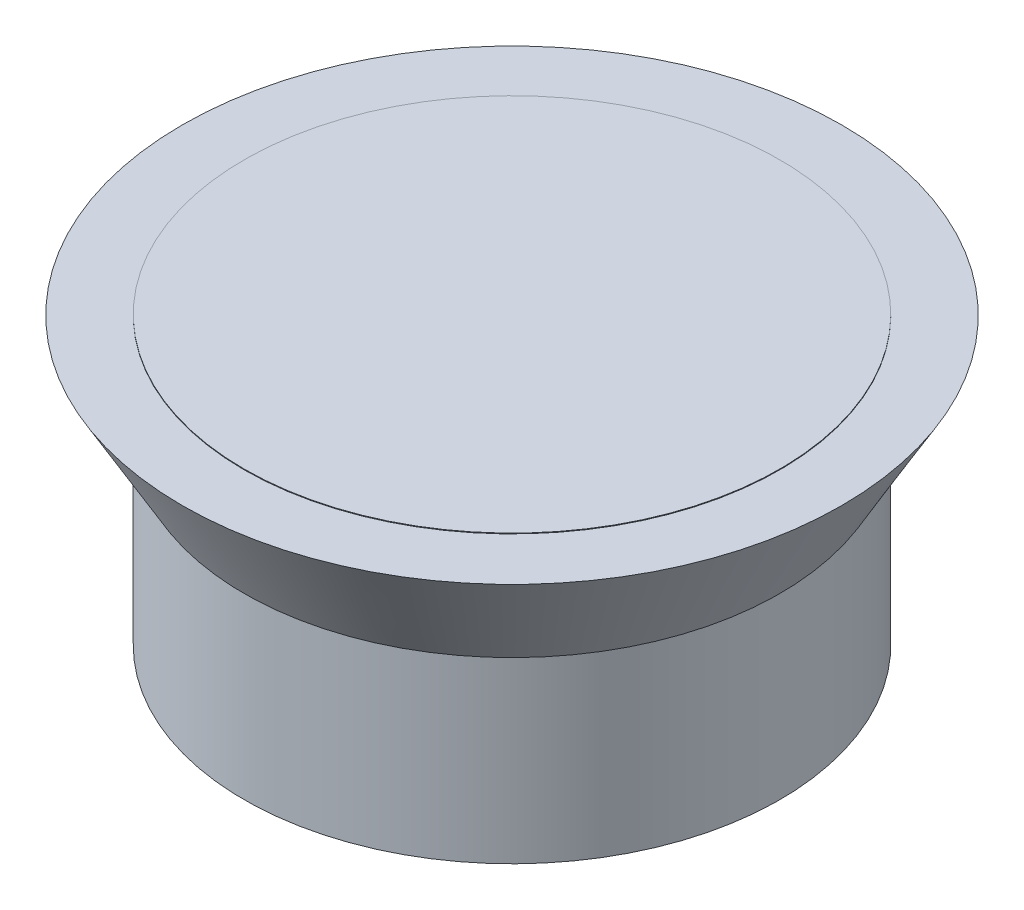
SolidWorks part; units mm, degrees
material "Custom Plastic"
ref_plane "Front Plane" through (0, 0, 0) normal (0, 0, 1) x (1, 0, 0)
ref_plane "Top Plane" through (0, 0, 0) normal (0, 1, 0) x (1, 0, 0)
ref_plane "Right Plane" through (0, 0, 0) normal (1, 0, 0) x (0, 0, -1)
sketch "Sketch1" plane through (0, 0, 0) normal (0, 0, 1) x (1, 0, 0)
  line L0 (0, 0) -> (0, 38.7866) construction
  line L1 (0, 0) -> (-9.525, 0)
  line L2 (-9.525, 0) -> (-9.525, 6.35)
  line L3 (-9.525, 6.35) -> (-11.7247, 10.16)
  line L4 (-11.7247, 10.16) -> (0, 10.16)
  line L5 (0, 10.16) -> (0, 0)
  dimension "D1" = 9.525
  dimension "D2" = 10.16
  dimension "D3" = 6.35
  dimension "D4" = 60
revolve "Revolve1" add sketch "Sketch1" angle 360 about L0
sketch "Sketch2" plane through (0, 10.16, 0) normal (0, 1, 0) x (1, 0, 0)
  circle A0 centre (0, 0) radius 9.525
  dimension "D1" = 19.05
extrude "Boss-Extrude1" add sketch "Sketch2" along normal blind 0.0254
